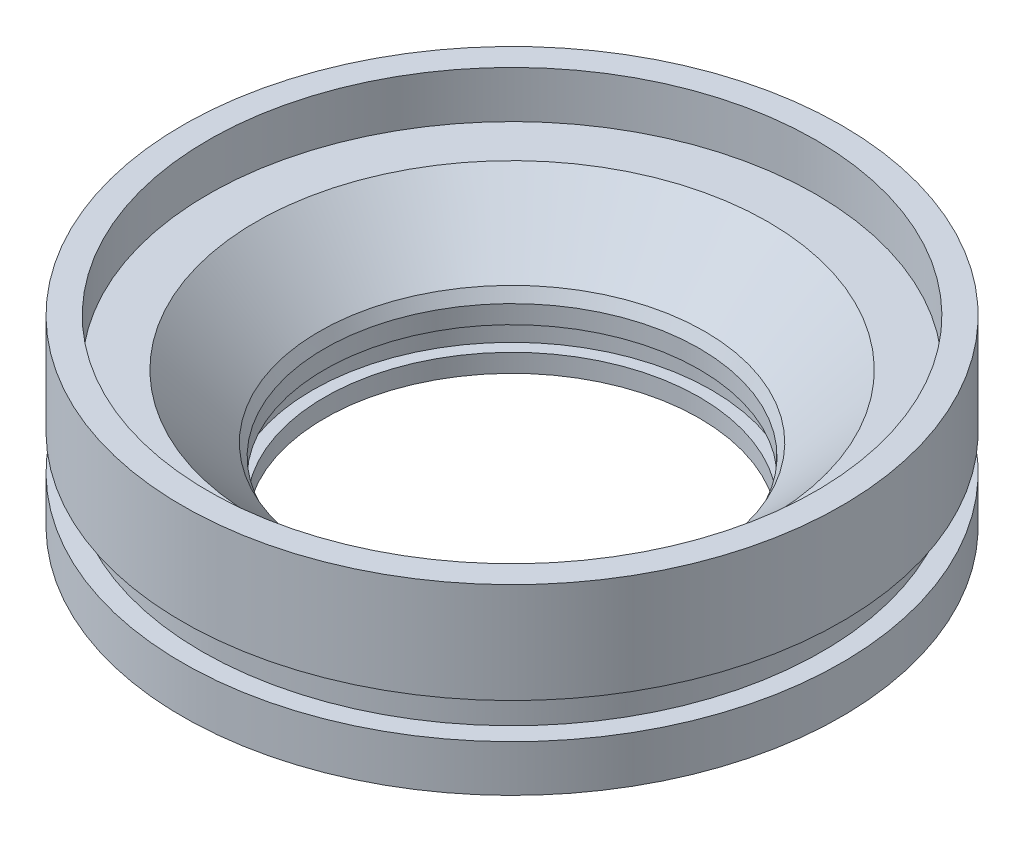
SolidWorks part; units mm, degrees
material "6061-T6 (SS)"
ref_plane "Front Plane" through (0, 0, 0) normal (0, 0, 1) x (1, 0, 0)
ref_plane "Top Plane" through (0, 0, 0) normal (0, 1, 0) x (1, 0, 0)
ref_plane "Right Plane" through (0, 0, 0) normal (1, 0, 0) x (0, 0, -1)
sketch "Sketch1" plane through (0, 0, 0) normal (0, 0, 1) x (1, 0, 0)
  line L0 (26.0731, 0) -> (26.0731, 2.54)
  line L1 (55, 0) -> (-55, 0) construction
  line L2 (26.0731, 2.54) -> (27.7723, 2.54)
  line L3 (27.7723, 2.54) -> (27.7723, 5.8674)
  line L4 (27.7723, 5.8674) -> (26.0731, 5.8674)
  line L5 (26.0731, 5.8674) -> (26.0731, 8.4074)
  line L6 (26.0731, 8.4074) -> (26.8351, 10.0686)
  line L7 (26.8351, 10.0686) -> (35.6387, 18.8722)
  line L8 (35.6387, 18.8722) -> (42.2935, 18.8722)
  line L9 (42.2935, 18.8722) -> (42.2935, 25.4)
  line L10 (42.2935, 25.4) -> (45.8597, 25.4)
  line L11 (45.8597, 25.4) -> (45.8597, 11.43)
  line L12 (45.8597, 11.43) -> (43.1419, 11.43)
  line L13 (43.1419, 11.43) -> (43.1419, 6.477)
  line L14 (43.1419, 6.477) -> (45.8597, 6.477)
  line L15 (45.8597, 6.477) -> (45.8597, 0)
  line L16 (45.8597, 0) -> (26.0731, 0)
  line L17 (0, 0) -> (0, 14.506) construction
  line L18 (0, -55) -> (0, 55) construction
  dimension "D1" = 45.8597
  dimension "D2" = 26.0731
  dimension "D3" = 25.4
  dimension "D4" = 13.97
  dimension "D5" = 4.953
  dimension "D6" = 2.7178
  dimension "D7" = 6.5278
  dimension "D8" = 42.2935
  dimension "D9" = 3.3274
  dimension "D10" = 2.54
  dimension "D11" = 135
  dimension "D12" = 6.6548
  dimension "D13" = 0.762
  dimension "D14" = 2.54
revolve "Revolve1" add sketch "Sketch1" angle 360 about L17
